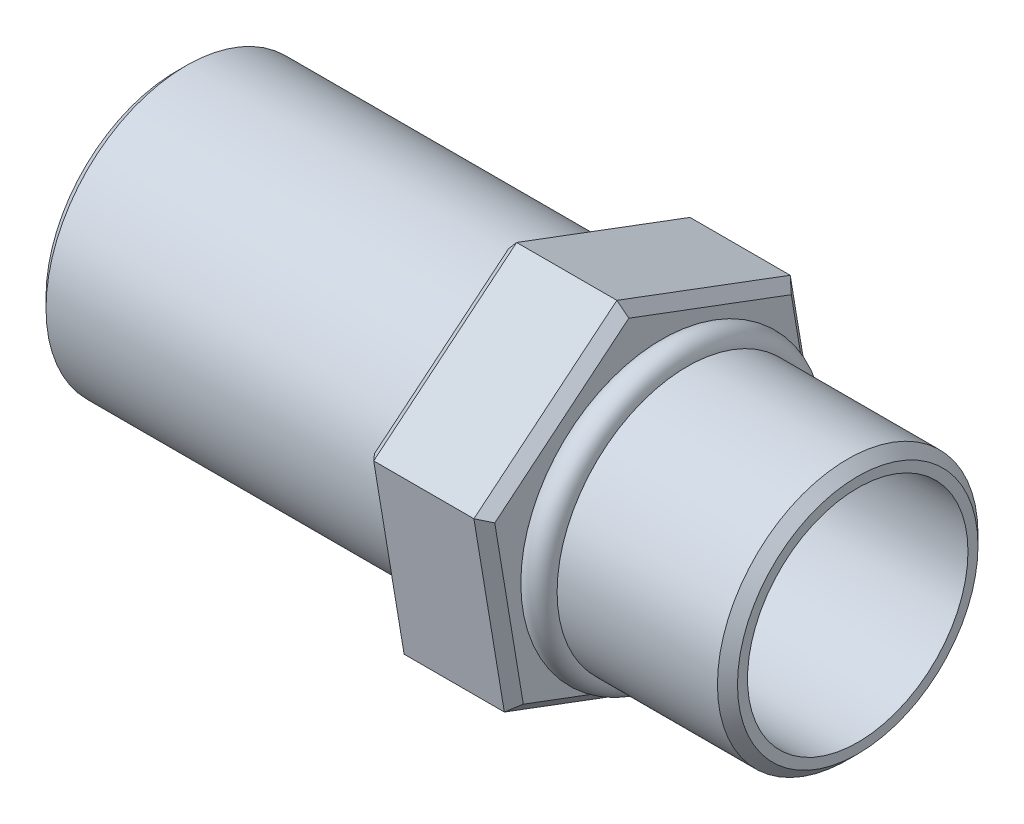
SolidWorks part; units mm, degrees
ref_plane "Front" through (0, 0, 0) normal (0, 0, 1) x (1, 0, 0)
ref_plane "Top" through (0, 0, 0) normal (0, 1, 0) x (1, 0, 0)
ref_plane "Right" through (0, 0, 0) normal (1, 0, 0) x (0, 0, -1)
sketch "Esquisse1" plane through (0, 0, 0) normal (1, 0, 0) x (0, 0, -1)
  circle A0 centre (0, 0) radius 0.65
  dimension "D1" = 1.3
extrude "Boss.-Extru.1" add sketch "Esquisse1" along normal blind 1
sketch "Esquisse2" plane through (0, 0, 0) normal (0, 0, 1) x (1, 0, 0)
  line L0 (1, 0.65) -> (0, 0.65) construction
  line L1 (0, 0.65) -> (0.15, 0.65)
  line L2 (1, 0) -> (0, 0) construction
  line L3 (1, -0.65) -> (1, 0.65) construction
  arc A0 (0, 0.65) -> (0.15, 0.65) centre (0.075, 0.65) cw
  dimension "D1" = 0.15
  dimension "D2" = 0
revolve "Révolution1" add sketch "Esquisse2" angle 360 about L2
sketch "Esquisse3" plane through (0, 0, 0) normal (-1, 0, 0) x (0, 0, 1)
  line L1 (0.7132, -0.5871) -> (0.865, 0.3241)
  line L2 (0.865, 0.3241) -> (0.1518, 0.9112)
  line L3 (0.1518, 0.9112) -> (-0.7132, 0.5871)
  line L4 (-0.7132, 0.5871) -> (-0.865, -0.3241)
  line L5 (-0.865, -0.3241) -> (-0.1518, -0.9112)
  line L6 (-0.1518, -0.9112) -> (0.7132, -0.5871)
  circle A0 centre (0, 0) radius 0.8 construction
  dimension "D1" = 1.6
extrude "Boss.-Extru.2" add sketch "Esquisse3" along normal blind 0.6
sketch "Esquisse4" plane through (-0.6, 0, 0) normal (-1, 0, 0) x (0, 0, 1)
  circle A0 centre (0, 0) radius 0.7
  dimension "D1" = 1.4
extrude "Boss.-Extru.3" add sketch "Esquisse4" along normal blind 1.8
chamfer "Chanfrein1" distance 0.05 angle 45 6 edges at (-0.6, -0.1315, 0.7891) (-0.6, 0.6177, 0.5084) (-0.6, 0.7491, -0.2807) (-0.6, 0.1315, -0.7891) (-0.6, -0.6177, -0.5084) (-0.6, -0.7491, 0.2807)
chamfer "Chanfrein2" distance 0.05 angle 45 6 edges at (0, 0.7491, -0.2807) (0, 0.6177, 0.5084) (0, -0.1315, 0.7891) (0, -0.7491, 0.2807) (0, -0.6177, -0.5084) (0, 0.1315, -0.7891)
sketch "Esquisse5" plane through (-2.4, 0, 0) normal (-1, 0, 0) x (0, 0, 1)
  circle A0 centre (0, 0) radius 0.575
  dimension "D1" = 1.15
extrude "Enlèv. mat.-Extru.1" cut sketch "Esquisse5" against normal blind 2.4
sketch "Esquisse6" plane through (1, 0, 0) normal (1, 0, 0) x (0, 0, -1)
  circle A0 centre (0, 0) radius 0.55
  dimension "D1" = 1.1
extrude "Enlèv. mat.-Extru.2" cut sketch "Esquisse6" against normal blind 2.4
chamfer "Chanfrein3" distance 0.05 angle 45 1 edges at (1, 0, -0.65)
chamfer "Chanfrein4" distance 0.05 angle 45 1 edges at (-2.4, 0, 0.7)
chamfer "Chanfrein5" distance 0.01 angle 45 1 edges at (-0.6, 0, 0.7)
sketch "Esquisse7" plane through (0, 0.6177, 0.5084) normal (0, 0.7721, 0.6355) x (1, 0, 0)
  line L0 (-0.55, 0) -> (-0.05, 0) construction
  line L1 (-0.55, 0.4619) -> (-0.55, -0.4619) construction
  line L2 (-0.05, -0.4619) -> (-0.05, 0.4619) construction
  circle A0 centre (-0.3, 0) radius 0.075
  dimension "D1" = 0.15
extrude "Boss.-Extru.4" add sketch "Esquisse7" against normal blind 1.5
scale "Echelle1" scale about origin uniform scaling yes scale factor 10
